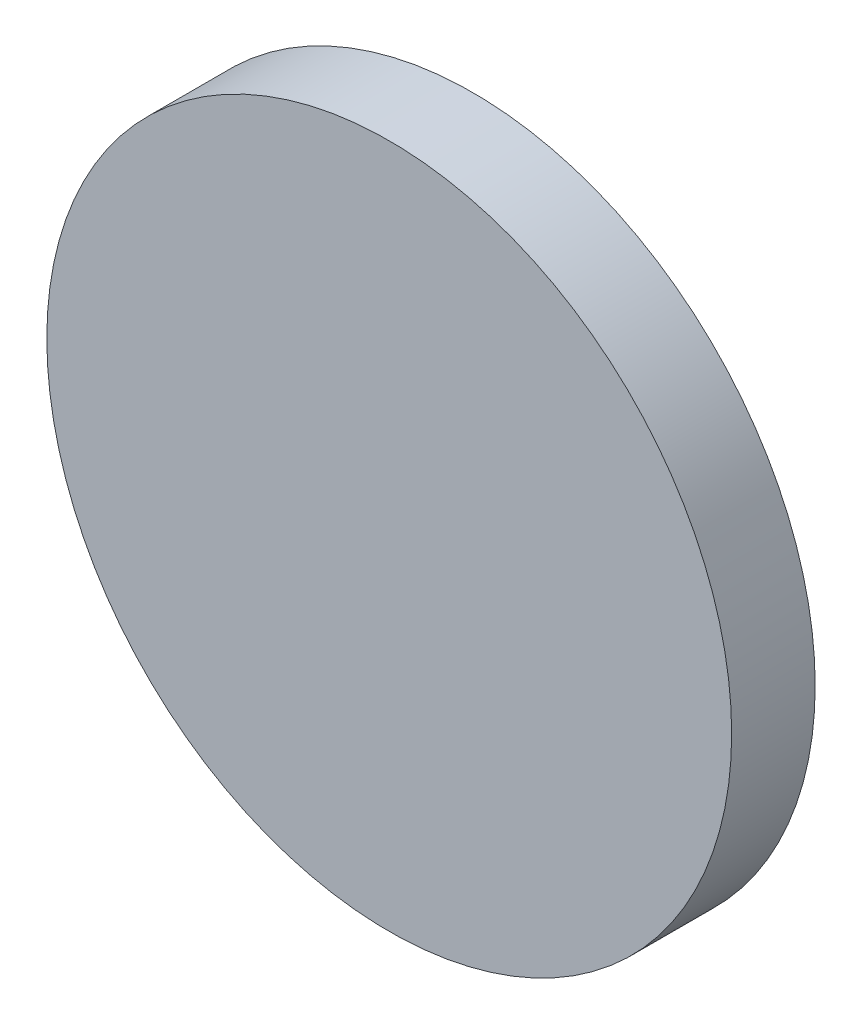
SolidWorks part; units mm, degrees
ref_plane "Front Plane" through (0, 0, 0) normal (0, 0, 1) x (1, 0, 0)
ref_plane "Top Plane" through (0, 0, 0) normal (0, 1, 0) x (1, 0, 0)
ref_plane "Right Plane" through (0, 0, 0) normal (1, 0, 0) x (0, 0, -1)
sketch "Sketch1" plane through (0, 0, 0) normal (0, 0, 1) x (1, 0, 0)
  circle A0 centre (0, 0) radius 20.5
  dimension "D1" = 41
extrude "Extrude1" add sketch "Sketch1" along normal blind 5
